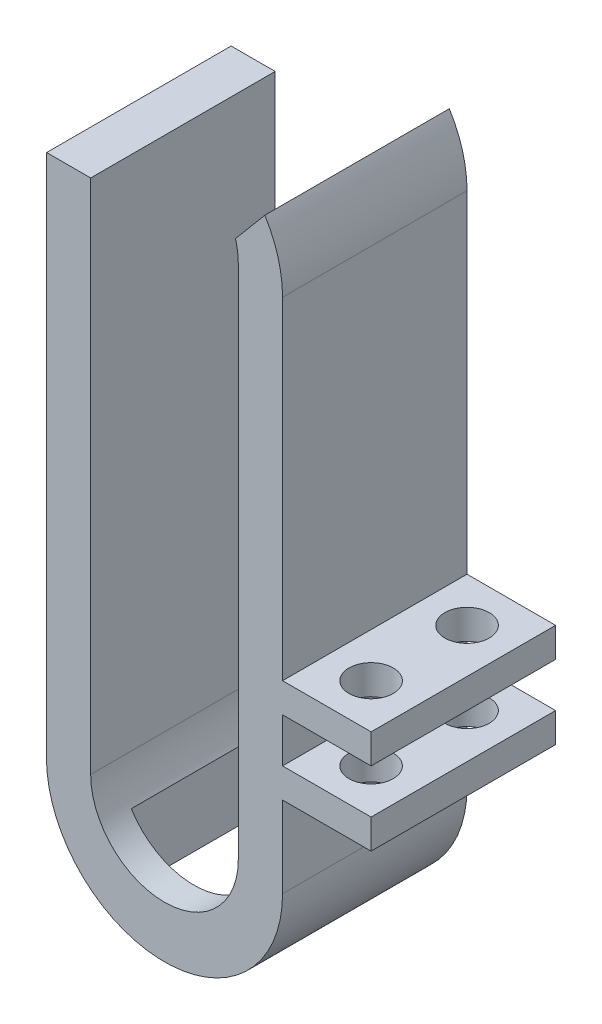
SolidWorks part; units mm, degrees
ref_plane "Front Plane" through (0, 0, 0) normal (0, 0, 1) x (1, 0, 0)
ref_plane "Top Plane" through (0, 0, 0) normal (0, 1, 0) x (1, 0, 0)
ref_plane "Right Plane" through (0, 0, 0) normal (1, 0, 0) x (0, 0, -1)
sketch "Sketch1" plane through (0, 0, 0) normal (0, 0, 1) x (1, 0, 0)
  line L0 (0, 17.5) -> (0, -17.5) construction
  line L1 (5, 17.5) -> (5, -17.5)
  line L2 (-5, 8.5) -> (-5, -17.5)
  line L3 (8, 17) -> (8, -18)
  line L4 (-8, 11.5) -> (-8, -18)
  line L6 (-8, 11.5) -> (-5, 8.5)
  line L9 (-5, 17.5) -> (-5, 8.5)
  line L10 (-8, 17) -> (-8, 11.5)
  line L11 (-6.105, 27.1604) -> (2.0351, 15.5351)
  line L12 (-5, 8.5) -> (2.0351, 15.5351)
  line L13 (-7.9844, 17.5) -> (7.9844, 17.5)
  line L14 (2.0351, 15.5351) -> (9.5686, 24.5132)
  arc A0 (5, 17.5) -> (-5, 17.5) centre (0, 17.5) ccw
  arc A1 (-5, -17.5) -> (5, -17.5) centre (0, -17.5) ccw
  arc A2 (-8, -18) -> (8, -18) centre (0, -18) ccw
  arc A3 (8, 17) -> (-8, 17) centre (0, 17) ccw
  point P2 (0, 0)
  dimension "D4" = 35
  dimension "D7" = 100
  dimension "D8" = 75
  dimension "D1" = 3
  dimension "D2" = 3
  dimension "D3" = 5
  dimension "D5" = 35
  dimension "D6" = 17
extrude "Boss-Extrude1" add sketch "Sketch1" along normal blind 12.5
sketch "Sketch2" plane through (8, 0, 0) normal (1, 0, 0) x (0, 0, -1)
  line L0 (0, 17) -> (0, -18) construction
  line L7 (-12.5, 17) -> (0, 17) construction
  line L8 (-12.5, 17) -> (-12.5, -18) construction
  line L9 (-12.5, -12.5) -> (0, -12.5)
  line L10 (-12.5, -12.5) -> (-12.5, -10.5)
  line L11 (-12.5, -10.5) -> (0, -10.5)
  line L12 (0, -12.5) -> (0, -10.5)
  line L13 (-12.5, -5.5) -> (0, -5.5)
  line L14 (-12.5, -5.5) -> (-12.5, -7.5)
  line L15 (-12.5, -7.5) -> (0, -7.5)
  line L16 (0, -5.5) -> (0, -7.5)
  dimension "D1" = 22.5
  dimension "D2" = 3
  dimension "D3" = 2
  dimension "D4" = 2
extrude "Boss-Extrude2" add sketch "Sketch2" along normal blind 6
sketch "Sketch3" plane through (0, -10.5, 0) normal (0, 1, 0) x (1, 0, 0)
  line L0 (14, 0) -> (8, 0) construction
  line L1 (8, -6.25) -> (14, -6.25) construction
  line L2 (8, 0) -> (8, -12.5) construction
  line L3 (14, 0) -> (14, -12.5) construction
  circle A1 centre (11, -3) radius 1.5
  circle A2 centre (11, -9.5) radius 1.5
  point P10 (11, -9.5)
  dimension "D1" = 3
  dimension "D2" = 3
  dimension "D3" = 3
extrude "Cut-Extrude1" cut sketch "Sketch3" against normal through all both and the other way through all
sketch "Sketch5" plane through (0, 0, 0) normal (0, 1, 0) x (1, 0, 0)
  line L1 (-4.25, -2) -> (4.25, -2)
  line L2 (-4.25, -2) -> (-4.25, -10.5)
  line L3 (-4.25, -10.5) -> (4.25, -10.5)
  line L4 (4.25, -2) -> (4.25, -10.5)
  line L5 (-5, -12.5) -> (5, -12.5) construction
  line L6 (-5, -12.5) -> (-5, 0) construction
  point P8 (0, -12.5)
  point P9 (0, -10.5)
  point P12 (-5, -6.25)
  point P13 (-4.25, -6.25)
  dimension "D1" = 8.5
  dimension "D2" = 8.5
extrude "Cut-Extrude2" cut sketch "Sketch5" against normal through all
